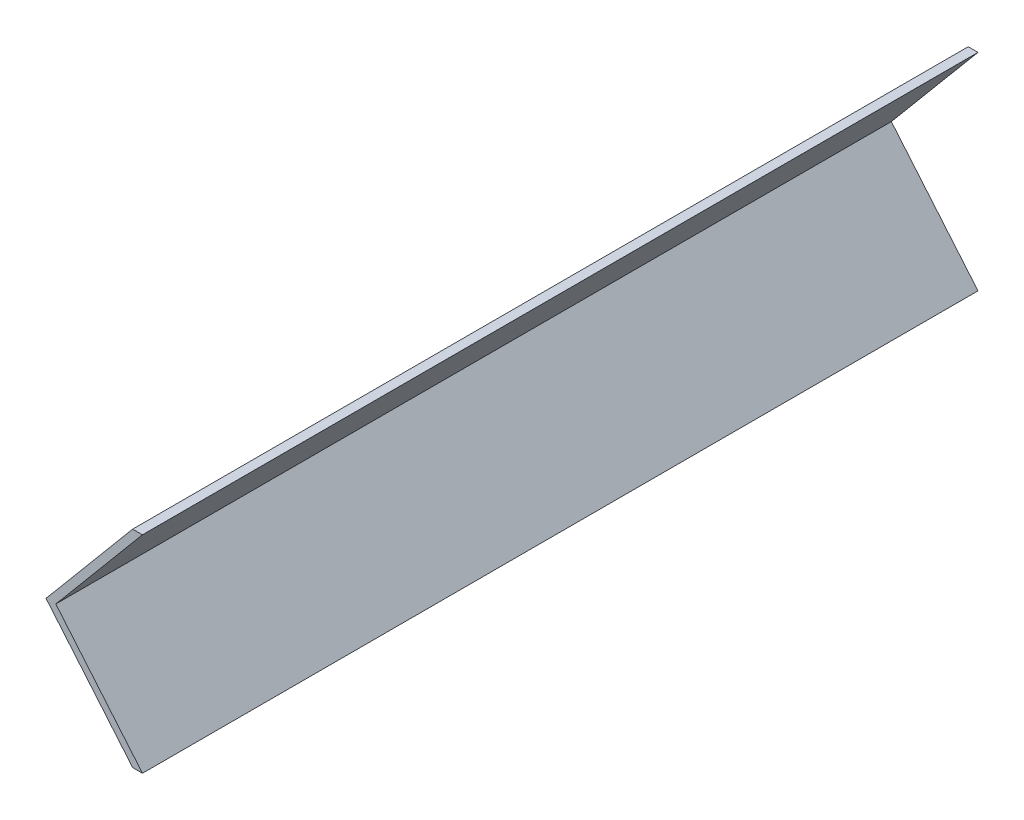
SolidWorks part; units mm, degrees
material "6061-T6 (SS)"
ref_plane "Front Plane" through (0, 0, 0) normal (0, 0, 1) x (1, 0, 0)
ref_plane "Top Plane" through (0, 0, 0) normal (0, 1, 0) x (1, 0, 0)
ref_plane "Right Plane" through (0, 0, 0) normal (1, 0, 0) x (0, 0, -1)
sketch "Sketch1" plane through (0, 0, 0) normal (0, 0, 1) x (1, 0, 0)
  line L0 (0, 0) -> (0, -82.2973) construction
  line L1 (0, 0) -> (-23.0752, -27.5)
  line L2 (-23.0752, -27.5) -> (0, -55)
  line L3 (0, 0) -> (2.6108, 0)
  line L5 (0, -55) -> (2.6108, -55)
  line L6 (2.6108, 0) -> (-20.4644, -27.5)
  line L7 (-20.4644, -27.5) -> (2.6108, -55)
  dimension "D1" = 55
  dimension "D2" = 2
  dimension "D3" = 100
extrude "Boss-Extrude1" add sketch "Sketch1" along normal blind 222.5
